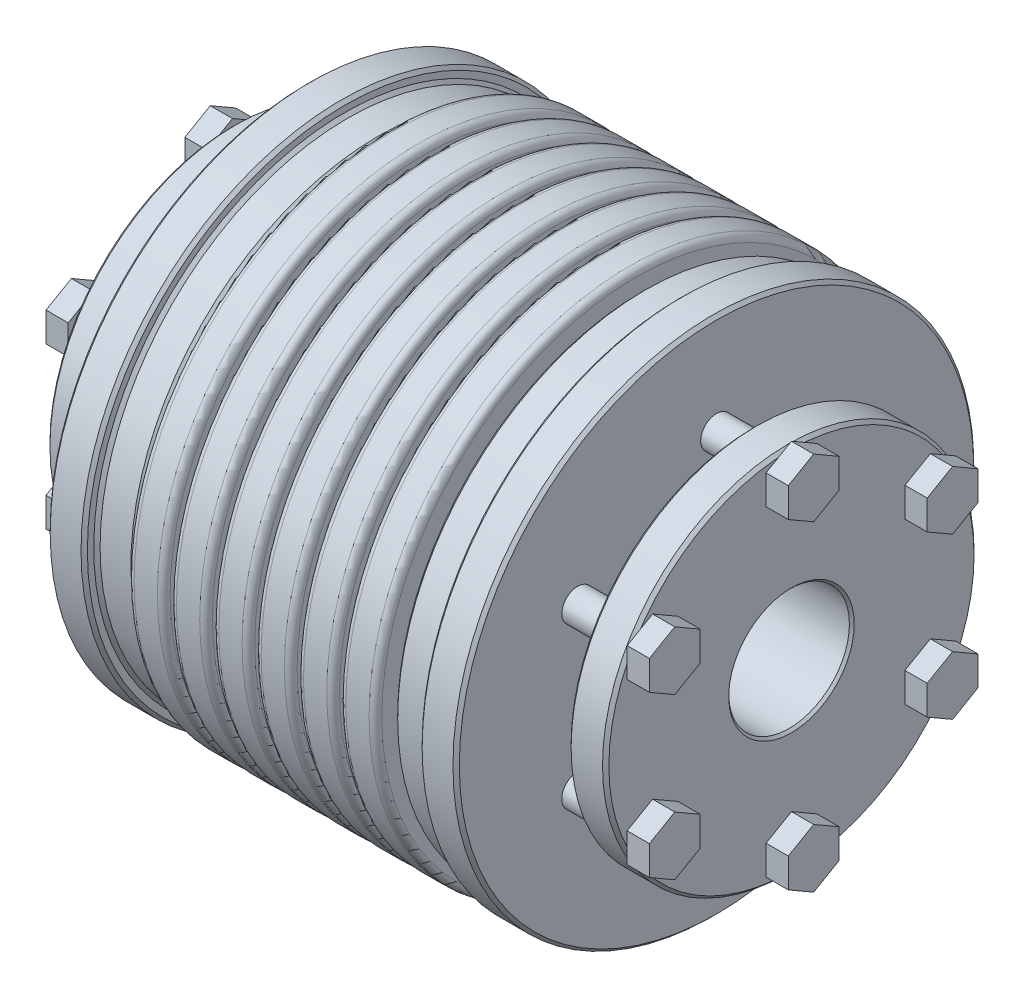
SolidWorks part; units mm, degrees
ref_plane "Front Plane" through (0, 0, 0) normal (0, 0, 1) x (1, 0, 0)
ref_plane "Top Plane" through (0, 0, 0) normal (0, 1, 0) x (1, 0, 0)
ref_plane "Right Plane" through (0, 0, 0) normal (1, 0, 0) x (0, 0, -1)
sketch "Sketch1" plane through (0, 0, 0) normal (1, 0, 0) x (0, 0, -1)
  circle A0 centre (0, 0) radius 41
  dimension "dim D" = 82
extrude "Boss-Extrude1" add sketch "Sketch1" along normal mid plane 88
sketch "Sketch2" plane through (44, 0, 0) normal (1, 0, 0) x (0, 0, -1)
  circle A0 centre (0, 0) radius 9.5
  dimension "dim d1" = 19
extrude "Cut-Extrude1" cut sketch "Sketch2" against normal blind 19
mirror "Mirror3" about plane through (0, 0, 0) normal (1, 0, 0) of "Cut-Extrude1"
chamfer "Chamfer1" distance 0.381 angle 45 4 edges at (-44, 0, -41) (44, 0, -41) (44, 0, -9.5) (-44, 0, -9.5)
ref_plane "L1" through (12, 0, 0) normal (1, 0, 0) x (0, 0, -1)
sketch "Sketch5" plane through (0, 0, 0) normal (1, 0, 0) x (0, 0, -1)
  line L0 (0, 9.881) -> (0, 41) construction
  circle A0 centre (0, 0) radius 9.881 construction
  circle A1 centre (0, 0) radius 25.4405
  circle A3 centre (0, 0) radius 41 construction
  point P9 (0, 25.4405)
extrude "Cut-Extrude2" cut sketch "Sketch5" against normal up to surface and the other way up to surface up to face at (-25, 0, -9.5) other way up to face at (25, 0, -9.5)
sketch "Sketch8" plane through (0, 0, 0) normal (0, 1, 0) x (1, 0, 0)
  line L0 (25, 25.4405) -> (-25, 25.4405) construction
  line L2 (-0.5, 27.4405) -> (0.5, 27.4405)
  line L3 (-0.5, 27.4405) -> (-0.5, 41)
  line L4 (-0.5, 41) -> (0.5, 41)
  line L5 (0, 27.4405) -> (0, 0) construction
  line L6 (0.5, 27.4405) -> (0.5, 41)
  line L7 (0, 0) -> (44, 0) construction
  line L8 (44, -40.619) -> (44, 40.619) construction
  line L9 (25, 9.5) -> (25, -9.5) construction
  line L10 (25, 9.5) -> (25, -9.5) construction
  line L11 (-44, -27.4405) -> (44, -27.4405) construction
  line L13 (0.5, 27.4405) -> (1.27, 27.4405) construction
  line L14 (-44, 40.619) -> (-44, -40.619) construction
  line L15 (6.1667, 27.4405) -> (7.1667, 27.4405)
  line L16 (6.1667, 27.4405) -> (6.1667, 41)
  line L17 (6.1667, 41) -> (7.1667, 41)
  line L18 (7.1667, 27.4405) -> (7.1667, 41)
  line L19 (12.8333, 27.4405) -> (13.8333, 27.4405)
  line L20 (12.8333, 27.4405) -> (12.8333, 41)
  line L21 (12.8333, 41) -> (13.8333, 41)
  line L22 (13.8333, 27.4405) -> (13.8333, 41)
  line L23 (19.5, 27.4405) -> (20.5, 27.4405)
  line L24 (19.5, 27.4405) -> (19.5, 41)
  line L25 (19.5, 41) -> (20.5, 41)
  line L26 (20.5, 27.4405) -> (20.5, 41)
  line L27 (-0.5, 27.4405) -> (6.1667, 27.4405) construction
  line L28 (0, 0) -> (0, -27.4405) construction
  dimension "D2" = 4
  dimension "D1" = 1
  dimension "D3" = 2
  dimension "Dim L2" = 41
revolve "Cut-Revolve1" cut sketch "Sketch8" angle 360 about L7
mirror "Mirror2" about plane through (0, 0, 0) normal (1, 0, 0) of "Cut-Revolve1"
fillet "Fillet1" radius 1 14 edges at (0.5, 0, 41) (-0.5, 0, 41) (20.5, 0, 41) (19.5, 0, 41) (13.8333, 0, 41) (12.8333, 0, 41) (7.1667, 0, 41) (6.1667, 0, 41) (-19.5, 0, 41) (-13.8333, 0, 41) (-12.8333, 0, 41) (-7.1667, 0, 41) (-6.1667, 0, 41) (-20.5, 0, 41)
fillet "Fillet2" radius 0.25 14 edges at (-12.8333, 0, 27.4405) (-6.1667, 0, 27.4405) (0.5, 0, 27.4405) (7.1667, 0, 27.4405) (13.8333, 0, 27.4405) (20.5, 0, 27.4405) (19.5, 0, 27.4405) (12.8333, 0, 27.4405) (6.1667, 0, 27.4405) (-0.5, 0, 27.4405) (-7.1667, 0, 27.4405) (-13.8333, 0, 27.4405) (-19.5, 0, 27.4405) (-20.5, 0, 27.4405)
sketch "Sketch9" plane through (0, 0, 0) normal (0, 0, 1) x (1, 0, 0)
  line L0 (20.5, 39) -> (26.3524, 39)
  line L1 (20.5, 40) -> (20.5, -40) construction
  line L2 (26.3524, 39) -> (26.3524, 41)
  line L3 (43.619, 41) -> (21.5, 41) construction
  line L4 (26.3524, 41) -> (32.2049, 41)
  line L5 (32.2049, 41) -> (32.2049, 20.2181)
  line L6 (32.2049, 20.2181) -> (38.0573, 21.25)
  line L7 (38.0573, 21.25) -> (38.0573, 29.25)
  line L8 (38.0573, 29.25) -> (44, 29.25)
  line L9 (44, -40.619) -> (44, 40.619) construction
  line L10 (44, 29.25) -> (44, 46)
  line L11 (44, 46) -> (20.5, 46)
  line L12 (20.5, 46) -> (20.5, 39)
  line L13 (38.0573, 21.25) -> (32.2049, 21.25) construction
  line L14 (43.619, 9.5) -> (43.619, 41) construction
  line L15 (43.619, 25.25) -> (38.0573, 25.25) construction
  line L16 (44, 0) -> (-44, 0) construction
  line L17 (-44, 40.619) -> (-44, -40.619) construction
  line L18 (0, 0) -> (0, -27.1776) construction
  line L19 (-43.619, 25.25) -> (-38.0573, 25.25) construction
  line L20 (-43.619, 9.5) -> (-43.619, 41) construction
  line L21 (-38.0573, 21.25) -> (-32.2049, 21.25) construction
  line L22 (-20.5, 46) -> (-20.5, 39)
  line L23 (-44, 46) -> (-20.5, 46)
  line L24 (-44, 29.25) -> (-44, 46)
  line L25 (-38.0573, 29.25) -> (-44, 29.25)
  line L26 (-38.0573, 21.25) -> (-38.0573, 29.25)
  line L27 (-32.2049, 20.2181) -> (-38.0573, 21.25)
  line L28 (-32.2049, 41) -> (-32.2049, 20.2181)
  line L29 (-26.3524, 41) -> (-32.2049, 41)
  line L30 (-26.3524, 39) -> (-26.3524, 41)
  line L31 (-20.5, 39) -> (-26.3524, 39)
  dimension "D1" = 5
  dimension "D2" = 2
  dimension "D3" = 4
  dimension "D4" = 4
  dimension "D5" = 10
revolve "Cut-Revolve2" cut sketch "Sketch9" angle 360 about L16
sketch "Sketch10" plane through (44, 0, 0) normal (1, 0, 0) x (0, 0, -1)
  line L0 (0, 21.25) -> (0, 29.25) construction
  line L1 (17.8671, 10.3156) -> (21.8671, 8.0062)
  line L2 (0, 20.6312) -> (4, 22.9406)
  line L3 (4, 22.9406) -> (4, 27.5594)
  line L4 (4, 27.5594) -> (0, 29.8688)
  line L5 (0, 29.8688) -> (-4, 27.5594)
  line L6 (-4, 27.5594) -> (-4, 22.9406)
  line L7 (-4, 22.9406) -> (0, 20.6312)
  line L8 (21.8671, 8.0062) -> (25.8671, 10.3156)
  line L9 (25.8671, 10.3156) -> (25.8671, 14.9344)
  line L10 (25.8671, 14.9344) -> (21.8671, 17.2438)
  line L11 (21.8671, 17.2438) -> (17.8671, 14.9344)
  line L12 (17.8671, 14.9344) -> (17.8671, 10.3156)
  line L13 (18.403, 10.625) -> (25.3312, 14.625) construction
  line L14 (17.8671, -10.3156) -> (17.8671, -14.9344)
  line L15 (17.8671, -14.9344) -> (21.8671, -17.2438)
  line L16 (21.8671, -17.2438) -> (25.8671, -14.9344)
  line L17 (25.8671, -14.9344) -> (25.8671, -10.3156)
  line L18 (25.8671, -10.3156) -> (21.8671, -8.0062)
  line L19 (21.8671, -8.0062) -> (17.8671, -10.3156)
  line L20 (18.403, -10.625) -> (25.3312, -14.625) construction
  line L21 (0, -20.6312) -> (-4, -22.9406)
  line L22 (-4, -22.9406) -> (-4, -27.5594)
  line L23 (-4, -27.5594) -> (0, -29.8688)
  line L24 (0, -29.8688) -> (4, -27.5594)
  line L25 (4, -27.5594) -> (4, -22.9406)
  line L26 (4, -22.9406) -> (0, -20.6312)
  line L27 (0, -21.25) -> (0, -29.25) construction
  line L28 (-17.8671, -10.3156) -> (-21.8671, -8.0062)
  line L29 (-21.8671, -8.0062) -> (-25.8671, -10.3156)
  line L30 (-25.8671, -10.3156) -> (-25.8671, -14.9344)
  line L31 (-25.8671, -14.9344) -> (-21.8671, -17.2438)
  line L32 (-21.8671, -17.2438) -> (-17.8671, -14.9344)
  line L33 (-17.8671, -14.9344) -> (-17.8671, -10.3156)
  line L34 (-18.403, -10.625) -> (-25.3312, -14.625) construction
  line L35 (-17.8671, 10.3156) -> (-17.8671, 14.9344)
  line L36 (-17.8671, 14.9344) -> (-21.8671, 17.2438)
  line L37 (-21.8671, 17.2438) -> (-25.8671, 14.9344)
  line L38 (-25.8671, 14.9344) -> (-25.8671, 10.3156)
  line L39 (-25.8671, 10.3156) -> (-21.8671, 8.0062)
  line L40 (-21.8671, 8.0062) -> (-17.8671, 10.3156)
  line L41 (-18.403, 10.625) -> (-25.3312, 14.625) construction
  circle A0 centre (0, 0) radius 25.25 construction
  circle A1 centre (0, 0) radius 21.25 construction
  circle A2 centre (0, 0) radius 21.25 construction
  circle A3 centre (0, 0) radius 29.25 construction
  circle A4 centre (0, 25.25) radius 4 construction
  circle A5 centre (21.8671, 12.625) radius 4 construction
  circle A6 centre (21.8671, -12.625) radius 4 construction
  circle A7 centre (0, -25.25) radius 4 construction
  circle A8 centre (-21.8671, -12.625) radius 4 construction
  circle A9 centre (-21.8671, 12.625) radius 4 construction
  point P10 (0, 25.25)
  point P24 (21.8671, 12.625)
  point P35 (21.8671, -12.625)
  point P46 (0, -25.25)
  point P57 (-21.8671, -12.625)
  point P68 (-21.8671, 12.625)
  dimension "D1" = 6
  dimension "Dim Hex Head Width" = 8
extrude "Boss-Extrude2" add sketch "Sketch10" along normal blind 3.5 separate body
sketch "Sketch11" plane through (47.5, 0, 0) normal (1, 0, 0) x (0, 0, -1)
  line L0 (0, 29.8688) -> (0, 20.6312) construction
  line L1 (17.8671, 10.3156) -> (25.8671, 14.9344) construction
  circle A0 centre (0, 25.25) radius 2.5
  circle A1 centre (21.8671, 12.625) radius 2.5
  circle A2 centre (21.8671, -12.625) radius 2.5
  circle A3 centre (0, -25.25) radius 2.5
  circle A4 centre (-21.8671, -12.625) radius 2.5
  circle A5 centre (-21.8671, 12.625) radius 2.5
  dimension "D1" = 6
  dimension "Dim M" = 5
extrude "Boss-Extrude3" add sketch "Sketch11" against normal up to surface (15.2951 mm away) up to face at (32.2049, 20.2181, 0)
mirror "Mirror5" about plane through (0, 0, 0) normal (1, 0, 0) of bodies 123 124 125 126 127 128
chamfer "Chamfer2" distance 0.5 angle 45 12 edges at (38.0573, 29.25, 0) (44, 29.25, 0) (32.2049, 41, 0) (26.3524, 41, 0) (20.5, 39, 0) (26.3524, 39, 0) (-44, 29.25, 0) (-38.0573, 29.25, 0) (-32.2049, 41, 0) (-26.3524, 41, 0) (-26.3524, 39, 0) (-20.5, 39, 0)
